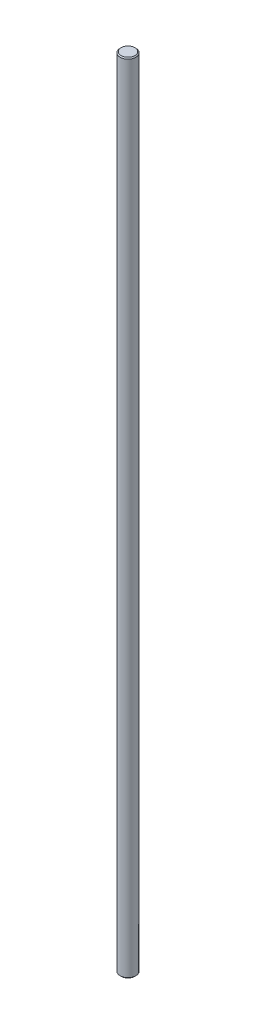
SolidWorks part; units mm, degrees
ref_plane "Front Plane" through (0, 0, 0) normal (0, 0, 1) x (1, 0, 0)
ref_plane "Top Plane" through (0, 0, 0) normal (0, 1, 0) x (1, 0, 0)
ref_plane "Right Plane" through (0, 0, 0) normal (1, 0, 0) x (0, 0, -1)
sketch "Sketch1" plane through (0, 0, 0) normal (0, 1, 0) x (1, 0, 0)
  circle A0 centre (0, 0) radius 4
  dimension "D1" = 8
extrude "Boss-Extrude1" add sketch "Sketch1" along normal blind 406.4
chamfer "Chamfer1" distance 0.5 angle 45 2 edges at (0, 0, 4) (0, 406.4, 4)
